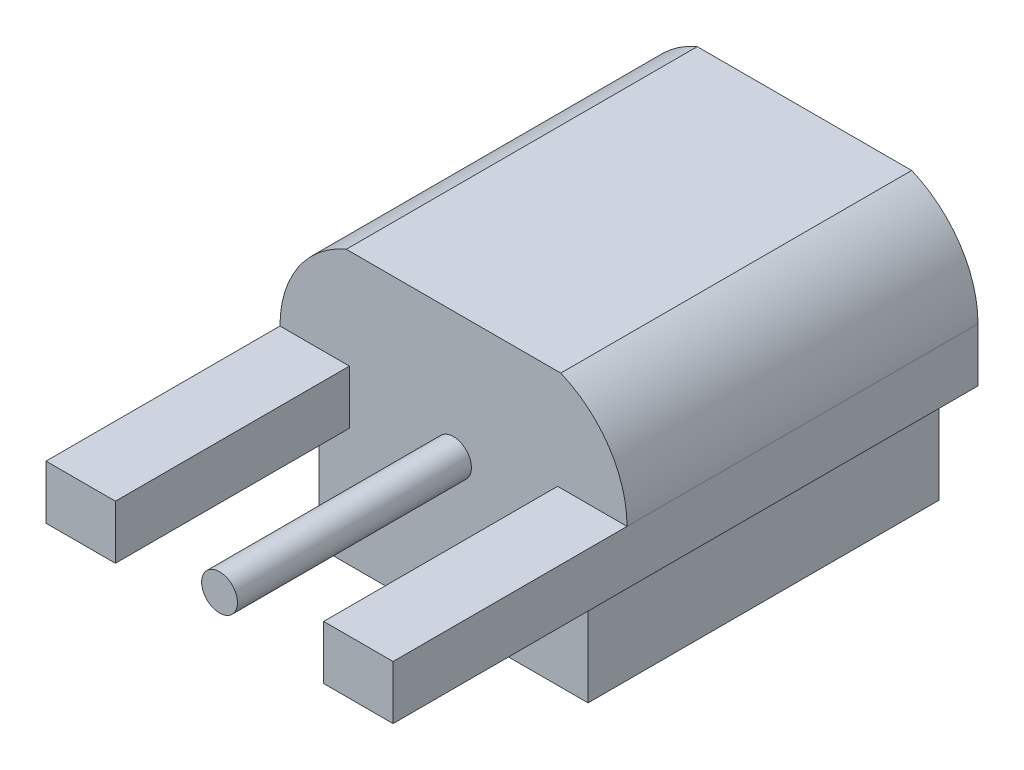
SolidWorks part; units mm, degrees
ref_plane "Front Plane" through (0, 0, 0) normal (0, 0, 1) x (1, 0, 0)
ref_plane "Top Plane" through (0, 0, 0) normal (0, 1, 0) x (1, 0, 0)
ref_plane "Right Plane" through (0, 0, 0) normal (1, 0, 0) x (0, 0, -1)
sketch "Sketch1" plane through (0, 0, 0) normal (0, 1, 0) x (1, 0, 0)
  line L0 (0, 3) -> (4.45, 3) construction
  line L1 (0, 0) -> (4.45, 0) construction
  line L2 (0, 0) -> (0, 7.5) construction
  line L3 (0, 7.5) -> (4.45, 7.5) construction
  line L4 (4.45, 0) -> (4.45, 7.5) construction
  line L5 (0.5, 3) -> (0.5, 0) construction
  line L6 (0.89, 3) -> (0.89, 0) construction
  line L7 (3.95, 3) -> (3.95, 0) construction
  line L8 (0.5, 2.0618) -> (0, 2.0618) construction
  line L9 (0.5, 1.5482) -> (0.89, 1.5482) construction
  line L10 (3.95, 1.7922) -> (4.45, 1.7922) construction
  line L11 (3.56, 3) -> (3.56, 0) construction
  line L12 (0.89, 3) -> (0.89, 0)
  line L13 (3.56, 2.7807) -> (3.95, 2.7807) construction
  line L14 (0.89, 0) -> (0, 0)
  line L15 (0, 0) -> (0, 7.5)
  line L16 (0, 7.5) -> (4.45, 7.5)
  line L17 (4.45, 7.5) -> (4.45, 0)
  line L18 (4.45, 0) -> (3.56, 0)
  line L19 (3.56, 0) -> (3.56, 3)
  line L20 (3.56, 3) -> (0.89, 3)
extrude "Boss-Extrude2" add sketch "Sketch1" along normal blind 0.69
sketch "Sketch3" plane through (0, 0, 0) normal (0, -1, 0) x (1, 0, 0)
  line L0 (4.45, -7.5) -> (0, -7.5) construction
  line L1 (0.5, -7.5) -> (3.95, -7.5)
  line L2 (0.5, -7.5) -> (0.5, -3)
  line L3 (0.5, -3) -> (3.95, -3)
  line L4 (3.95, -7.5) -> (3.95, -3)
  line L5 (0.5, -5.0796) -> (0, -5.0796) construction
  line L6 (0, -7.5) -> (0, 0) construction
  line L7 (3.95, -4.726) -> (4.45, -4.726) construction
  line L8 (4.45, 0) -> (4.45, -7.5) construction
  line L9 (0.89, -3) -> (3.56, -3) construction
extrude "Boss-Extrude3" add sketch "Sketch3" along normal blind 1.52
sketch "Sketch4" plane through (0, 0, -3) normal (0, 0, 1) x (1, 0, 0)
  line L0 (2.225, 0.345) -> (3.56, 0) construction
  line L1 (2.225, 0.345) -> (0.89, 0.69) construction
  circle A0 centre (2.225, 0.345) radius 0.2297
extrude "Boss-Extrude4" add sketch "Sketch4" along normal blind 3 separate body
sketch "Sketch5" plane through (0, 0, -7.5) normal (0, 0, -1) x (-1, 0, 0)
  line L0 (-4.45, 0.69) -> (0, 0.69) construction
  line L1 (-3.6, 0.69) -> (-3.6, 1.9674) construction
  line L2 (-0.85, 1.9674) -> (-0.85, 0.69) construction
  line L3 (-4.45, 0.69) -> (-3.6, 0.69) construction
  line L4 (-3.6, 1.9674) -> (-0.85, 1.9674)
  line L5 (-0.85, 0.69) -> (0, 0.69) construction
  line L6 (0, 0.69) -> (-4.45, 0.69)
  arc A0 (-4.45, 0.69) -> (-3.6, 1.9674) centre (-3.0651, 0.69) cw
  arc A1 (0, 0.69) -> (-0.85, 1.9674) centre (-1.3849, 0.69) ccw
extrude "Boss-Extrude5" add sketch "Sketch5" against normal blind 4.5
sketch "Sketch6" plane through (0, 0, -7.5) normal (0, 0, -1) x (-1, 0, 0)
  circle A0 centre (-2.225, 0.345) radius 1.19
  circle A1 centre (-2.225, 0.345) radius 0.2297 construction
extrude "Cut-Extrude1" cut sketch "Sketch6" against normal blind 3
